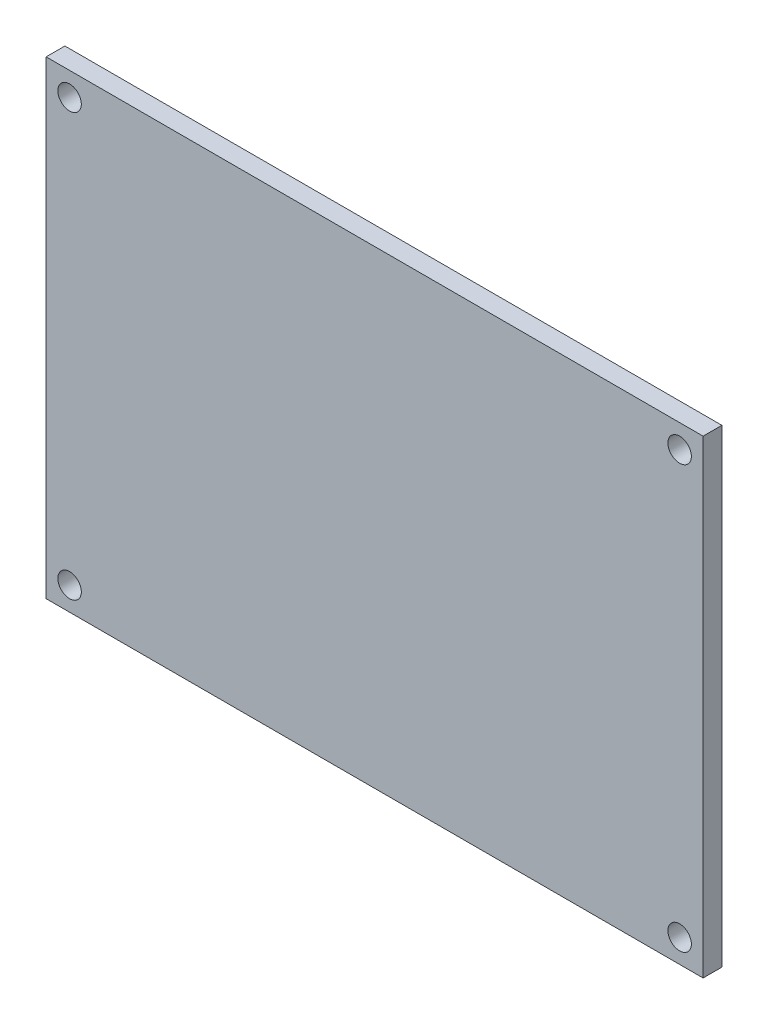
SolidWorks part; units mm, degrees
material "Acrylic (Medium-high impact)"
ref_plane "Front Plane" through (0, 0, 0) normal (0, 0, 1) x (1, 0, 0)
ref_plane "Top Plane" through (0, 0, 0) normal (0, 1, 0) x (1, 0, 0)
ref_plane "Right Plane" through (0, 0, 0) normal (1, 0, 0) x (0, 0, -1)
sketch "Sketch1" plane through (0, 0, 0) normal (0, 0, 1) x (1, 0, 0)
  line L1 (-98.1814, 44.3946) -> (43.8186, 44.3946)
  line L2 (-98.1814, 44.3946) -> (-98.1814, -57.6054)
  line L3 (-98.1814, -57.6054) -> (43.8186, -57.6054)
  line L4 (43.8186, 44.3946) -> (43.8186, -57.6054)
  circle A0 centre (-92.1814, 38.3946) radius 2.5
  circle A1 centre (37.8186, 38.3946) radius 2.5
  circle A2 centre (37.8186, -51.6054) radius 2.5
  circle A3 centre (-92.1814, -51.6054) radius 2.5
extrude "Boss-Extrude1" add sketch "Sketch1" along normal blind 4
sketch "Sketch2" plane through (0, 0, 4) normal (0, 0, 1) x (1, 0, 0)
  line L0 (-97.1814, 43.3946) -> (-97.1814, -56.6054)
  line L1 (-98.1814, 44.3946) -> (43.8186, 44.3946)
  line L2 (-98.1814, 44.3946) -> (-98.1814, -57.6054)
  line L3 (-98.1814, -57.6054) -> (43.8186, -57.6054)
  line L4 (43.8186, 44.3946) -> (43.8186, -57.6054)
  line L5 (-97.1814, -56.6054) -> (42.8186, -56.6054)
  line L6 (42.8186, 43.3946) -> (42.8186, -56.6054)
  line L7 (-97.1814, 43.3946) -> (42.8186, 43.3946)
  dimension "D1" = 1
extrude "Cut-Extrude1" cut sketch "Sketch2" against normal through all
